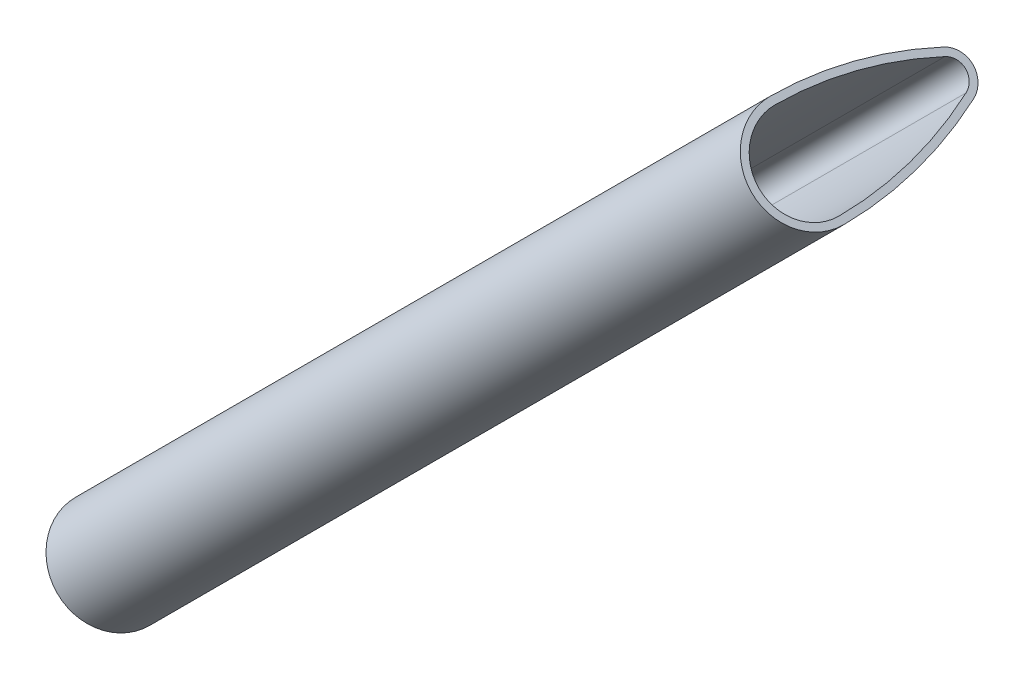
SolidWorks part; units mm, degrees
ref_plane "Front Plane" through (0, 0, 0) normal (0, 0, 1) x (1, 0, 0)
ref_plane "Top Plane" through (0, 0, 0) normal (0, 1, 0) x (1, 0, 0)
ref_plane "Right Plane" through (0, 0, 0) normal (1, 0, 0) x (0, 0, -1)
ref_plane "Plane1" through (33.0861, 33.0861, 4.0937) normal (-0.7044, -0.7044, -0.0872) x (0.7071, -0.7071, 0)
sketch "Sketch1" plane through (33.0861, 33.0861, 4.0937) normal (-0.7044, -0.7044, -0.0872) x (0.7071, -0.7071, 0)
  arc A0 (1.275, -31.6884) -> (-1.275, -31.6884) centre (0, -31.1101) cw
  arc A1 (-1.275, -31.6884) -> (-3.9, -19.6196) centre (25.4989, -19.5451) cw
  arc A2 (-3.9, -19.6196) -> (3.9, -19.6133) centre (0, -19.6097) cw
  arc A3 (3.9, -19.6133) -> (1.275, -31.6884) centre (-25.4989, -19.5451) cw
  arc A4 (-4.5, -19.6141) -> (-1.8214, -31.9362) centre (25.4989, -19.5451) ccw
  arc A5 (-1.8214, -31.9362) -> (1.8214, -31.9362) centre (0, -31.1101) ccw
  arc A6 (4.5, -19.6141) -> (1.8214, -31.9362) centre (-25.4999, -19.5448) cw
  arc A7 (-4.5, -19.6141) -> (4.5, -19.6141) centre (0, -19.61) cw
extrude "Boss-Extrude1" add sketch "Sketch1" against normal blind 96.6742
